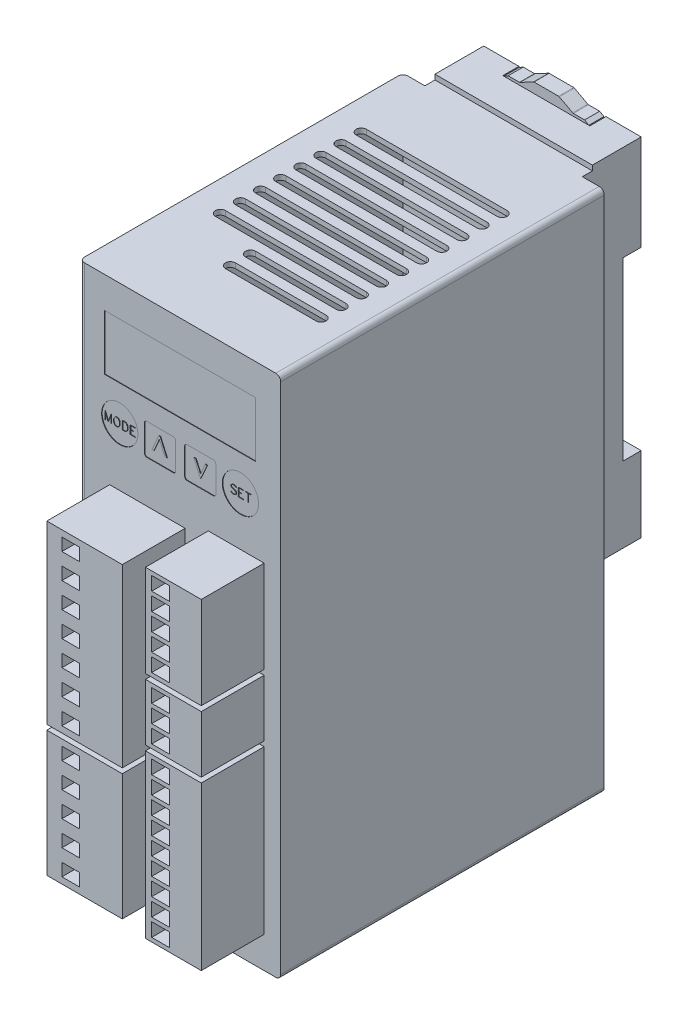
SolidWorks part; units mm, degrees
ref_plane "정면" through (0, 0, 0) normal (0, 0, 1) x (1, 0, 0)
ref_plane "윗면" through (0, 0, 0) normal (0, 1, 0) x (1, 0, 0)
ref_plane "우측면" through (0, 0, 0) normal (1, 0, 0) x (0, 0, -1)
sketch "스케치1" plane through (0, 0, 0) normal (0, 0, 1) x (1, 0, 0)
  line L0 (15, 5.5) -> (-15, -5.5) construction
  line L1 (-15, 5.5) -> (15, 5.5) construction
  line L2 (-15, 5.5) -> (-15, -5.5) construction
  line L3 (-15, -5.5) -> (15, -5.5) construction
  line L4 (15, 5.5) -> (15, -5.5) construction
  line L6 (-20, 11.7) -> (20, 11.7)
  line L7 (-20, 11.7) -> (-20, -92.3)
  line L8 (-20, -92.3) -> (20, -92.3)
  line L9 (20, 11.7) -> (20, -92.3)
  point P4 (0, 0)
  point P10 (0, 11.7)
  dimension "D1" = 11
  dimension "D2" = 30
  dimension "D3" = 40
  dimension "D4" = 11.7
  dimension "D5" = 104
extrude "보스-돌출1" add sketch "스케치1" against normal blind 64.3
shell "쉘6" thickness 1
sketch "스케치6" plane through (0, 0, -64.3) normal (0, 0, -1) x (-1, 0, 0)
  line L4 (20, -92.3) -> (20, 11.7)
  line L5 (20, 11.7) -> (-20, 11.7)
  line L6 (-20, 11.7) -> (-20, -92.3)
  line L7 (-20, -92.3) -> (20, -92.3)
  line L8 (20, -92.3) -> (20, 11.7)
  line L9 (20, 11.7) -> (-20, 11.7)
  line L10 (-20, 11.7) -> (-20, -92.3)
  line L11 (-20, -92.3) -> (20, -92.3)
  dimension "D1" = 0
extrude "보스-돌출4" add sketch "스케치6" against normal blind 1
sketch "스케치2" plane through (0, 0, 0) normal (0, 0, 1) x (1, 0, 0)
  line L0 (-15, 5.5) -> (15, 5.5) construction
  line L1 (15, 5.5) -> (15, -5.5) construction
  line L2 (-15, -5.5) -> (15, -5.5) construction
  line L3 (-15, 5.5) -> (-15, -5.5) construction
  line L4 (-15, 5.5) -> (15, 5.5)
  line L5 (15, 5.5) -> (15, -5.5)
  line L6 (-15, -5.5) -> (15, -5.5)
  line L7 (-15, 5.5) -> (-15, -5.5)
extrude "컷-돌출1" cut sketch "스케치2" against normal blind 0.1
sketch "스케치3" plane through (0, 0, 0) normal (0, 0, 1) x (1, 0, 0)
  line L0 (-14, -24) -> (1, -24)
  line L1 (-14, -85) -> (-5.1, -85)
  line L2 (-14, -60) -> (-14, -85)
  line L3 (-14, -85) -> (1, -85)
  line L4 (-14, -60) -> (1, -60)
  line L5 (1, -85) -> (1, -60)
  line L6 (-7.5, -63.75) -> (-11, -63.75)
  line L7 (-7.5, -63.75) -> (-7.5, -61.25)
  line L8 (-7.5, -61.25) -> (-11, -61.25)
  line L9 (-11, -61.25) -> (-11, -63.75)
  line L10 (-7.5, -68.75) -> (-11, -68.75)
  line L11 (-7.5, -68.75) -> (-7.5, -66.25)
  line L12 (-7.5, -66.25) -> (-11, -66.25)
  line L13 (-11, -66.25) -> (-11, -68.75)
  line L14 (-7.5, -73.75) -> (-11, -73.75)
  line L15 (-7.5, -73.75) -> (-7.5, -71.25)
  line L16 (-7.5, -71.25) -> (-11, -71.25)
  line L17 (-11, -71.25) -> (-11, -73.75)
  line L18 (-7.5, -78.75) -> (-11, -78.75)
  line L19 (-7.5, -78.75) -> (-7.5, -76.25)
  line L20 (-7.5, -76.25) -> (-11, -76.25)
  line L21 (-11, -76.25) -> (-11, -78.75)
  line L22 (-7.5, -83.75) -> (-11, -83.75)
  line L23 (-7.5, -83.75) -> (-7.5, -81.25)
  line L24 (-7.5, -81.25) -> (-11, -81.25)
  line L25 (-11, -81.25) -> (-11, -83.75)
  line L26 (-14, -24) -> (-14, -59)
  line L27 (-14, -59) -> (1, -59)
  line L28 (1, -59) -> (1, -24)
  line L29 (-7.5, -27.75) -> (-11, -27.75)
  line L30 (-7.5, -27.75) -> (-7.5, -25.25)
  line L31 (-7.5, -25.25) -> (-11, -25.25)
  line L32 (-11, -25.25) -> (-11, -27.75)
  line L33 (-7.5, -32.75) -> (-11, -32.75)
  line L34 (-7.5, -32.75) -> (-7.5, -30.25)
  line L35 (-7.5, -30.25) -> (-11, -30.25)
  line L36 (-11, -30.25) -> (-11, -32.75)
  line L37 (-7.5, -37.75) -> (-11, -37.75)
  line L38 (-7.5, -37.75) -> (-7.5, -35.25)
  line L39 (-7.5, -35.25) -> (-11, -35.25)
  line L40 (-11, -35.25) -> (-11, -37.75)
  line L41 (-7.5, -42.75) -> (-11, -42.75)
  line L42 (-7.5, -42.75) -> (-7.5, -40.25)
  line L43 (-7.5, -40.25) -> (-11, -40.25)
  line L44 (-11, -40.25) -> (-11, -42.75)
  line L45 (-7.5, -47.75) -> (-11, -47.75)
  line L46 (-7.5, -47.75) -> (-7.5, -45.25)
  line L47 (-7.5, -45.25) -> (-11, -45.25)
  line L48 (-11, -45.25) -> (-11, -47.75)
  line L49 (-7.5, -52.75) -> (-11, -52.75)
  line L50 (-7.5, -52.75) -> (-7.5, -50.25)
  line L51 (-7.5, -50.25) -> (-11, -50.25)
  line L52 (-11, -50.25) -> (-11, -52.75)
  line L53 (-7.5, -57.75) -> (-11, -57.75)
  line L54 (-7.5, -57.75) -> (-7.5, -55.25)
  line L55 (-7.5, -55.25) -> (-11, -55.25)
  line L56 (-11, -55.25) -> (-11, -57.75)
  line L57 (5.6, -22.15) -> (5.6, -40.45)
  line L58 (6.85, -22.95) -> (6.85, -25.65)
  line L59 (6.85, -26.45) -> (6.85, -29.15)
  line L60 (6.85, -29.95) -> (6.85, -32.65)
  line L61 (6.85, -33.45) -> (6.85, -36.15)
  line L62 (6.85, -36.95) -> (6.85, -39.65)
  line L63 (10.35, -22.95) -> (10.35, -25.65)
  line L64 (10.35, -26.45) -> (10.35, -29.15)
  line L65 (10.35, -29.95) -> (10.35, -32.65)
  line L66 (10.35, -33.45) -> (10.35, -36.15)
  line L67 (10.35, -36.95) -> (10.35, -39.65)
  line L68 (16.7, -22.15) -> (16.7, -40.45)
  line L69 (5.6, -22.15) -> (16.7, -22.15)
  line L70 (6.85, -22.95) -> (10.35, -22.95)
  line L71 (6.85, -25.65) -> (10.35, -25.65)
  line L72 (6.85, -26.45) -> (10.35, -26.45)
  line L73 (6.85, -29.15) -> (10.35, -29.15)
  line L74 (6.85, -29.95) -> (10.35, -29.95)
  line L75 (6.85, -32.65) -> (10.35, -32.65)
  line L76 (6.85, -33.45) -> (10.35, -33.45)
  line L77 (6.85, -36.15) -> (10.35, -36.15)
  line L78 (6.85, -36.95) -> (10.35, -36.95)
  line L79 (6.85, -39.65) -> (10.35, -39.65)
  line L80 (5.6, -40.45) -> (16.7, -40.45)
  line L81 (5.6, -41.45) -> (16.7, -41.45)
  line L82 (5.6, -41.45) -> (5.6, -52.75)
  line L83 (6.85, -42.25) -> (6.85, -44.95)
  line L84 (6.85, -45.75) -> (6.85, -48.45)
  line L85 (6.85, -49.25) -> (6.85, -51.95)
  line L86 (10.35, -42.25) -> (10.35, -44.95)
  line L87 (10.35, -45.75) -> (10.35, -48.45)
  line L88 (10.35, -49.25) -> (10.35, -51.95)
  line L89 (16.7, -41.45) -> (16.7, -52.75)
  line L90 (6.85, -42.25) -> (10.35, -42.25)
  line L91 (6.85, -44.95) -> (10.35, -44.95)
  line L92 (6.85, -45.75) -> (10.35, -45.75)
  line L93 (6.85, -48.45) -> (10.35, -48.45)
  line L94 (6.85, -49.25) -> (10.35, -49.25)
  line L95 (6.85, -51.95) -> (10.35, -51.95)
  line L96 (5.6, -52.75) -> (16.7, -52.75)
  line L97 (5.6, -53.75) -> (16.7, -53.75)
  line L98 (5.6, -53.75) -> (5.6, -86.05)
  line L99 (6.85, -54.55) -> (6.85, -57.25)
  line L100 (6.85, -58.05) -> (6.85, -60.75)
  line L101 (6.85, -61.55) -> (6.85, -64.25)
  line L102 (6.85, -65.05) -> (6.85, -67.75)
  line L103 (6.85, -68.55) -> (6.85, -71.25)
  line L104 (6.85, -72.05) -> (6.85, -74.75)
  line L105 (6.85, -75.55) -> (6.85, -78.25)
  line L106 (6.85, -79.05) -> (6.85, -81.75)
  line L107 (6.85, -82.55) -> (6.85, -85.25)
  line L108 (10.35, -54.55) -> (10.35, -57.25)
  line L109 (10.35, -58.05) -> (10.35, -60.75)
  line L110 (10.35, -61.55) -> (10.35, -64.25)
  line L111 (10.35, -65.05) -> (10.35, -67.75)
  line L112 (10.35, -68.55) -> (10.35, -71.25)
  line L113 (10.35, -72.05) -> (10.35, -74.75)
  line L114 (10.35, -75.55) -> (10.35, -78.25)
  line L115 (10.35, -79.05) -> (10.35, -81.75)
  line L116 (10.35, -82.55) -> (10.35, -85.25)
  line L117 (16.7, -53.75) -> (16.7, -86.05)
  line L118 (6.85, -54.55) -> (10.35, -54.55)
  line L119 (6.85, -57.25) -> (10.35, -57.25)
  line L120 (6.85, -58.05) -> (10.35, -58.05)
  line L121 (6.85, -60.75) -> (10.35, -60.75)
  line L122 (6.85, -61.55) -> (10.35, -61.55)
  line L123 (6.85, -64.25) -> (10.35, -64.25)
  line L124 (6.85, -65.05) -> (10.35, -65.05)
  line L125 (6.85, -67.75) -> (10.35, -67.75)
  line L126 (6.85, -68.55) -> (10.35, -68.55)
  line L127 (6.85, -71.25) -> (10.35, -71.25)
  line L128 (6.85, -72.05) -> (10.35, -72.05)
  line L129 (6.85, -74.75) -> (10.35, -74.75)
  line L130 (6.85, -75.55) -> (10.35, -75.55)
  line L131 (6.85, -78.25) -> (10.35, -78.25)
  line L132 (6.85, -79.05) -> (10.35, -79.05)
  line L133 (6.85, -81.75) -> (10.35, -81.75)
  line L134 (6.85, -82.55) -> (10.35, -82.55)
  line L135 (6.85, -85.25) -> (10.35, -85.25)
  line L136 (5.6, -86.05) -> (16.7, -86.05)
extrude "보스-돌출3" add sketch "스케치3" along normal blind 12.5 contours L27 L28 L0 L26 L56 L55 L54 L53 L52 L51 L50 L49 L48 L47 L46 L45 L44 L43 L42 L41 L40 L39 L38 L37 L36 L35 L34 L33 L32 L31 L30 L29 | L57 L80 L68 L69 L71 L58 L70 L63 L73 L59 L72 L64 L75 L60 L74 L65 L77 L61 L76 L66 L79 L62 L78 L67 | L82 L96 L89 L81 L91 L83 L90 L86 L93 L84 L92 L87 L95 L85 L94 L88 | L98 L136 L117 L97 L119 L99 L118 L108 L121 L100 L120 L109 L123 L101 L122 L110 L125 L102 L124 L111 L127 L103 L126 L112 L129 L104 L128 L113 L131 L105 L130 L114 L133 L106 L132 L115 L135 L107 L134 L116 | L3 L5 L4 L2 L1 L25 L24 L23 L22 L21 L20 L19 L18 L17 L16 L15 L14 L13 L12 L11 L10 L9 L8 L7 L6
sketch "스케치4" plane through (0, 0, 0) normal (0, 0, 1) x (1, 0, 0)
  line L0 (-6.6, -15.6) -> (-1.4, -15.6)
  line L1 (-6.6, -9.4) -> (-1.4, -9.4)
  line L2 (7.1, -9.9) -> (7.1, -15.1)
  line L3 (0.9, -9.9) -> (0.9, -15.1)
  line L4 (-7.1, -9.9) -> (-7.1, -15.1)
  line L5 (-0.9, -9.9) -> (-0.9, -15.1)
  line L6 (1.4, -9.4) -> (6.6, -9.4)
  line L7 (6.6, -15.6) -> (1.4, -15.6)
  arc A0 (-7.1, -15.1) -> (-6.6, -15.6) centre (-6.6, -15.1) ccw
  arc A1 (7.1, -9.9) -> (6.6, -9.4) centre (6.6, -9.9) ccw
  arc A2 (-6.6, -9.4) -> (-7.1, -9.9) centre (-6.6, -9.9) ccw
  arc A3 (-0.9, -9.9) -> (-1.4, -9.4) centre (-1.4, -9.9) ccw
  arc A4 (-1.4, -15.6) -> (-0.9, -15.1) centre (-1.4, -15.1) ccw
  circle A5 centre (-12, -12.5) radius 3.6
  circle A6 centre (12, -12.5) radius 3.6
  arc A7 (1.4, -9.4) -> (0.9, -9.9) centre (1.4, -9.9) ccw
  arc A8 (0.9, -15.1) -> (1.4, -15.6) centre (1.4, -15.1) ccw
  arc A9 (6.6, -15.6) -> (7.1, -15.1) centre (6.6, -15.1) ccw
extrude "컷-돌출2" cut sketch "스케치4" against normal blind 0.1
sketch "스케치7" plane through (0, 11.7, 0) normal (0, 1, 0) x (1, 0, 0)
  line L0 (14, 15) -> (-4, 15)
  line L1 (14, 13) -> (-4, 13)
  line L2 (14, 19) -> (-4, 19)
  line L3 (14, 17) -> (-4, 17)
  line L4 (14, 23) -> (-14, 23)
  line L5 (14, 21) -> (-14, 21)
  line L6 (14, 27) -> (-14, 27)
  line L7 (14, 25) -> (-14, 25)
  line L8 (14, 31) -> (-14, 31)
  line L9 (14, 29) -> (-14, 29)
  line L10 (14, 35) -> (-14, 35)
  line L11 (14, 33) -> (-14, 33)
  line L12 (14, 39) -> (-14, 39)
  line L13 (14, 37) -> (-14, 37)
  line L14 (14, 43) -> (-14, 43)
  line L15 (14, 41) -> (-14, 41)
  line L16 (14, 47) -> (-14, 47)
  line L17 (14, 45) -> (-14, 45)
  line L18 (14, 51) -> (-14, 51)
  line L19 (14, 49) -> (-14, 49)
  arc A0 (-4, 15) -> (-4, 13) centre (-4, 14) ccw
  arc A1 (14, 13) -> (14, 15) centre (14, 14) ccw
  arc A2 (-4, 19) -> (-4, 17) centre (-4, 18) ccw
  arc A3 (14, 17) -> (14, 19) centre (14, 18) ccw
  arc A4 (-14, 23) -> (-14, 21) centre (-14, 22) ccw
  arc A5 (14, 21) -> (14, 23) centre (14, 22) ccw
  arc A6 (-14, 27) -> (-14, 25) centre (-14, 26) ccw
  arc A7 (14, 25) -> (14, 27) centre (14, 26) ccw
  arc A8 (-14, 31) -> (-14, 29) centre (-14, 30) ccw
  arc A9 (14, 29) -> (14, 31) centre (14, 30) ccw
  arc A10 (-14, 35) -> (-14, 33) centre (-14, 34) ccw
  arc A11 (14, 33) -> (14, 35) centre (14, 34) ccw
  arc A12 (-14, 39) -> (-14, 37) centre (-14, 38) ccw
  arc A13 (14, 37) -> (14, 39) centre (14, 38) ccw
  arc A14 (-14, 43) -> (-14, 41) centre (-14, 42) ccw
  arc A15 (14, 41) -> (14, 43) centre (14, 42) ccw
  arc A16 (-14, 47) -> (-14, 45) centre (-14, 46) ccw
  arc A17 (14, 45) -> (14, 47) centre (14, 46) ccw
  arc A18 (-14, 51) -> (-14, 49) centre (-14, 50) ccw
  arc A19 (14, 49) -> (14, 51) centre (14, 50) ccw
extrude "컷-돌출3" cut sketch "스케치7" against normal blind 1
sketch "스케치9" plane through (0, -92.3, 0) normal (0, -1, 0) x (1, 0, 0)
  line L20 (4, -49) -> (-4, -49)
  line L21 (4, -51) -> (-4, -51)
  line L22 (4, -45) -> (-4, -45)
  line L23 (4, -47) -> (-4, -47)
  line L24 (4, -41) -> (-4, -41)
  line L25 (4, -43) -> (-4, -43)
  line L26 (14, -37) -> (-4, -37)
  line L27 (14, -39) -> (-4, -39)
  line L28 (14, -33) -> (-4, -33)
  line L29 (14, -35) -> (-4, -35)
  line L30 (14, -29) -> (-4, -29)
  line L31 (14, -31) -> (-4, -31)
  line L32 (14, -25) -> (-4, -25)
  line L33 (14, -27) -> (-4, -27)
  line L34 (14, -21) -> (-4, -21)
  line L35 (14, -23) -> (-4, -23)
  line L36 (14, -17) -> (-4, -17)
  line L37 (14, -19) -> (-4, -19)
  line L38 (14, -13) -> (-4, -13)
  line L39 (14, -15) -> (-4, -15)
  line L40 (8.5, -40) -> (12.5, -40)
  line L41 (12.5, -40) -> (12.5, -47.5)
  line L42 (8.5, -40) -> (8.5, -47.5)
  line L43 (8.5, -47.5) -> (12.5, -47.5)
  arc A20 (-4, -49) -> (-4, -51) centre (-4, -50) ccw
  arc A21 (4, -51) -> (4, -49) centre (4, -50) ccw
  arc A22 (-4, -45) -> (-4, -47) centre (-4, -46) ccw
  arc A23 (4, -47) -> (4, -45) centre (4, -46) ccw
  arc A24 (-4, -41) -> (-4, -43) centre (-4, -42) ccw
  arc A25 (4, -43) -> (4, -41) centre (4, -42) ccw
  arc A26 (-4, -37) -> (-4, -39) centre (-4, -38) ccw
  arc A27 (14, -39) -> (14, -37) centre (14, -38) ccw
  arc A28 (-4, -33) -> (-4, -35) centre (-4, -34) ccw
  arc A29 (14, -35) -> (14, -33) centre (14, -34) ccw
  arc A30 (-4, -29) -> (-4, -31) centre (-4, -30) ccw
  arc A31 (14, -31) -> (14, -29) centre (14, -30) ccw
  arc A32 (-4, -25) -> (-4, -27) centre (-4, -26) ccw
  arc A33 (14, -27) -> (14, -25) centre (14, -26) ccw
  arc A34 (-4, -21) -> (-4, -23) centre (-4, -22) ccw
  arc A35 (14, -23) -> (14, -21) centre (14, -22) ccw
  arc A36 (-4, -17) -> (-4, -19) centre (-4, -18) ccw
  arc A37 (14, -19) -> (14, -17) centre (14, -18) ccw
  arc A38 (-4, -13) -> (-4, -15) centre (-4, -14) ccw
  arc A39 (14, -15) -> (14, -13) centre (14, -14) ccw
extrude "컷-돌출4" cut sketch "스케치9" against normal blind 1
sketch "스케치10" plane through (0, 0, -0.1) normal (0, 0, 1) x (1, 0, 0)
  text T0 "MODE" font "Simplex" height in points 6
extrude "보스-돌출5" add sketch "스케치10" along normal blind 0.1
sketch "스케치11" plane through (0, 0, -0.1) normal (0, 0, 1) x (1, 0, 0)
  text T0 "SET" font "Simplex" height in points 6
extrude "보스-돌출6" add sketch "스케치11" along normal blind 0.1
sketch "스케치12" plane through (0, 0, -0.1) normal (0, 0, 1) x (1, 0, 0)
  text T0 "^" font "Century Gothic" height in points 15
extrude "보스-돌출7" add sketch "스케치12" along normal blind 0.1
sketch "스케치13" plane through (0, 0, -0.1) normal (0, 0, 1) x (1, 0, 0)
  text T0 "v" font "Century Gothic" height in points 15
extrude "보스-돌출8" add sketch "스케치13" along normal blind 0.1
sketch "스케치14" plane through (0, 0, 0) normal (1, 0, 0) x (0, 0, -1)
  line L0 (66.3, 12.7) -> (66.3, 11.7)
  line L1 (66.3, -55.3) -> (66.3, -56.3)
  line L2 (76, 12.7) -> (76, -6.3)
  line L3 (76, -41.3) -> (76, -56.3)
  line L4 (72.4, -6.3) -> (72.4, -41.3)
  line L6 (66.3, 12.7) -> (76, 12.7)
  line L7 (66.3, -56.3) -> (76, -56.3)
  line L8 (72.4, -41.3) -> (76, -41.3)
  line L9 (72.4, -6.3) -> (76, -6.3)
  line L10 (64.3, -55.3) -> (66.3, -55.3)
  line L12 (66.3, 11.7) -> (64.3, 11.7)
  line L13 (64.3, 11.7) -> (64.3, -55.3)
  dimension "D1" = 15
extrude "보스-돌출9" add sketch "스케치14" along normal mid plane 31.3
sketch "스케치15" plane through (0, 0, -76) normal (0, 0, -1) x (-1, 0, 0)
  line L1 (-13.5, -45.8) -> (13.5, -45.8)
  line L2 (-13.5, -45.8) -> (-13.5, -54.3)
  line L3 (-13.5, -54.3) -> (13.5, -54.3)
  line L4 (13.5, -45.8) -> (13.5, -54.3)
  point P4 (0, -45.8)
  dimension "D1" = 27
  dimension "D2" = 8.5
  dimension "D3" = 2
extrude "컷-돌출5" cut sketch "스케치15" against normal blind 5.5
sketch "스케치16" plane through (0, 0, -76) normal (0, 0, -1) x (-1, 0, 0)
  line L0 (-15.65, -41.3) -> (15.65, -41.3) construction
  line L1 (-11.6, -41.3) -> (-5, -41.3)
  line L2 (-11.6, -41.3) -> (-11.6, -39.3)
  line L3 (-11.6, -39.3) -> (-5, -39.3)
  line L4 (-5, -41.3) -> (-5, -39.3)
  line L5 (-15.65, -41.3) -> (15.65, -41.3) construction
  line L6 (5, -41.3) -> (11.6, -41.3)
  line L7 (5, -41.3) -> (5, -39.3)
  line L8 (5, -39.3) -> (11.6, -39.3)
  line L9 (11.6, -41.3) -> (11.6, -39.3)
  line L10 (-5, -40.3) -> (5, -40.3) construction
  point P14 (0, -40.3)
  dimension "D1" = 2
  dimension "D2" = 6.6
  dimension "D3" = 10
extrude "보스-돌출10" add sketch "스케치16" against normal blind 2.6
chamfer "모따기2" distance 1.5 angle 45 2 edges at (-8.3, -39.3, -76) (8.3, -39.3, -76)
sketch "스케치17" plane through (0, 0, -76) normal (0, 0, -1) x (-1, 0, 0)
  line L1 (-7.5, 17.0932) -> (7.5, 17.0932)
  line L2 (-7.5, 17.0932) -> (-7.5, -10.8534)
  line L3 (-7.5, -10.8534) -> (7.5, -10.8534)
  line L4 (7.5, 17.0932) -> (7.5, -10.8534)
  point P4 (0, -10.8534)
  dimension "D1" = 15
extrude "컷-돌출6" cut sketch "스케치17" against normal blind 3.2
sketch "스케치18" plane through (0, 0, -76) normal (0, 0, -1) x (-1, 0, 0)
  line L1 (-8.65, 14.7) -> (8.65, 14.7)
  line L2 (-8.65, 14.7) -> (-8.65, 10.4)
  line L3 (-8.65, 10.4) -> (8.65, 10.4)
  line L4 (8.65, 14.7) -> (8.65, 10.4)
  point P4 (0, 10.4)
  dimension "D1" = 4.3
  dimension "D2" = 17.3
extrude "컷-돌출7" cut sketch "스케치18" against normal up to surface (3.2 mm away) up to face at (0, 3.2, -72.8)
sketch "스케치19" plane through (0, 0, -72.8) normal (0, 0, -1) x (-1, 0, 0)
  line L0 (-7.6, 13.2) -> (-5.3753, 13.2)
  line L1 (-2.4247, 14.7) -> (2.4247, 14.7)
  line L2 (8.45, 10.6) -> (8.45, 12.7)
  line L3 (-8.45, 10.6) -> (-8.45, 12.7)
  line L4 (-2.5664, 14.6644) -> (-5.2336, 13.2356)
  line L5 (2.5664, 14.6644) -> (5.2336, 13.2356)
  line L6 (7.6, 13.2) -> (5.3753, 13.2)
  line L7 (-5.3753, 13.2) -> (-7.6, 13.2)
  line L8 (-7.3, 10.6) -> (-7.3, -7.8)
  line L10 (-7.3, -7.8) -> (7.3, -7.8)
  line L11 (7.3, -7.8) -> (7.3, 10.6)
  line L12 (-8.45, 10.6) -> (-7.3, 10.6)
  line L13 (8.45, 10.6) -> (7.3, 10.6)
  line L14 (8.65, 10.4) -> (7.5, 10.4) construction
  line L15 (8.65, 12.7) -> (-8.65, 12.7) construction
  line L16 (7.6, 13.2) -> (8.45, 12.7)
  line L17 (-7.6, 13.2) -> (-8.45, 12.7)
  arc A0 (-5.3753, 13.2) -> (-5.2336, 13.2356) centre (-5.3753, 13.5) ccw
  arc A3 (-2.4247, 14.7) -> (-2.5664, 14.6644) centre (-2.4247, 14.4) ccw
  arc A4 (2.5664, 14.6644) -> (2.4247, 14.7) centre (2.4247, 14.4) ccw
  arc A5 (5.2336, 13.2356) -> (5.3753, 13.2) centre (5.3753, 13.5) ccw
  dimension "D1" = 1.5
  dimension "D2" = 0.2
  dimension "D3" = 0.2
  dimension "D6" = 0.2
  dimension "D7" = 0.2
extrude "보스-돌출14" add sketch "스케치19" along normal blind 3 contours L10 L11 L8 M8 | L13 L2 L3 L12 L8 L11 M4 M8 | A5 L5 A4 L1 A3 L4 A0 L0 L17 L16 L6 M4
chamfer "모따기3" distance 2.5 angle 45 1 edges at (0, -7.8, -75.8)
fillet "필렛1" radius 1 5 edges at (-20, -40.3, -64.3) (-20, -40.3, 0) (20, -92.3, -32.15) (19, -40.3, -1) (20, 11.7, -32.15)
sketch "스케치20" plane through (0, 0, -72.4) normal (0, 0, -1) x (-1, 0, 0)
  line L0 (1.5, -17.3) -> (1.5, -26.3)
  line L1 (-1.5, -17.3) -> (-1.5, -26.3)
  arc A0 (1.5, -17.3) -> (-1.5, -17.3) centre (0, -17.3) ccw
  arc A1 (-1.5, -26.3) -> (1.5, -26.3) centre (0, -26.3) ccw
  dimension "D1" = 3
  dimension "D2" = 12
  dimension "D3" = 30
extrude "컷-돌출8" cut sketch "스케치20" against normal up to surface (8.1 mm away) up to face at (4.3764, -26.2, -64.3)
